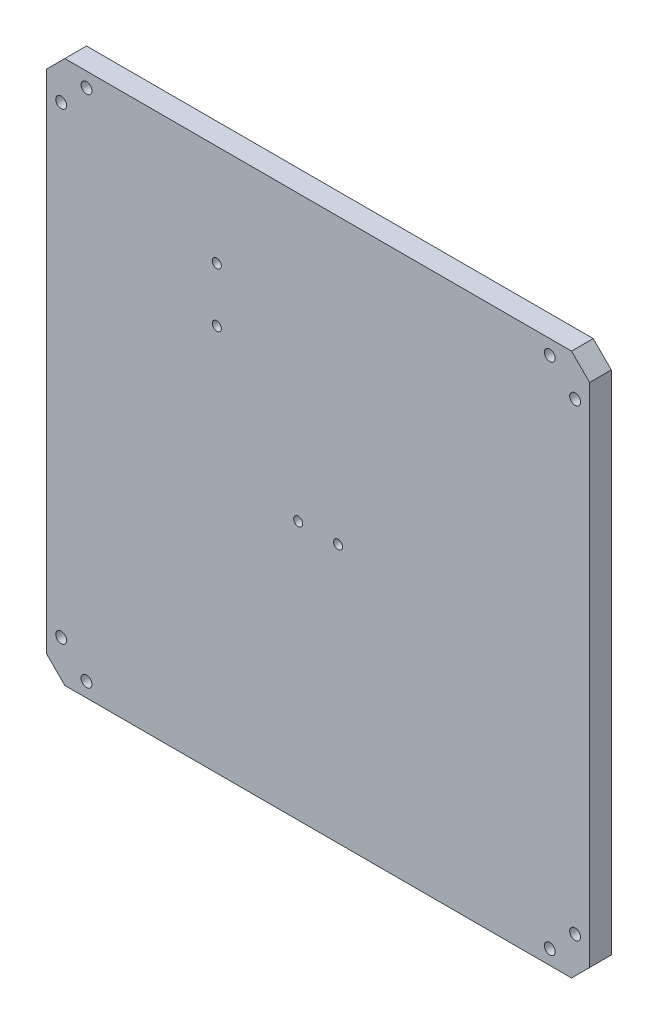
SolidWorks part; units mm, degrees
ref_plane "前视基准面" through (0, 0, 0) normal (0, 0, 1) x (1, 0, 0)
ref_plane "上视基准面" through (0, 0, 0) normal (0, 1, 0) x (1, 0, 0)
ref_plane "右视基准面" through (0, 0, 0) normal (1, 0, 0) x (0, 0, -1)
sketch "草图1" plane through (0, 0, 0) normal (0, 0, 1) x (1, 0, 0)
  line L1 (75, -75) -> (-75, -75)
  line L2 (75, -75) -> (75, 75)
  line L3 (75, 75) -> (-75, 75)
  line L4 (-75, -75) -> (-75, 75)
  line L5 (75, -75) -> (-75, 75) construction
  line L6 (75, 75) -> (-75, -75) construction
  point P0 (0, 0)
  dimension "D1" = 150
  dimension "D2" = 150
extrude "凸台-拉伸1" add sketch "草图1" along normal blind 6
chamfer "倒角1" distance 5 angle 45 4 edges at (75, -75, 3) (-75, -75, 3) (-75, 75, 3) (75, 75, 3)
sketch "草图2" plane through (0, 0, 6) normal (0, 0, 1) x (1, 0, 0)
  line L0 (75, -70) -> (75, 70) construction
  line L1 (70, 75) -> (-70, 75) construction
  line L2 (0, 110.4594) -> (0, -112.1687) construction
  circle A0 centre (64, 71) radius 1.5
  circle A1 centre (71, 64) radius 1.5
  circle A2 centre (-71, 64) radius 1.5
  circle A3 centre (-64, 71) radius 1.5
  dimension "D1" = 3
  dimension "D2" = 3
  dimension "D3" = 4
  dimension "D4" = 11
  dimension "D5" = 4
  dimension "D6" = 11
extrude "切除-拉伸1" cut sketch "草图2" against normal blind 10
sketch "草图3" plane through (0, 0, 0) normal (0, 0, -1) x (-1, 0, 0)
  line L0 (75, 70) -> (75, -70) construction
  line L1 (-70, 75) -> (70, 75) construction
  circle A0 centre (64, 71) radius 2.85
  circle A1 centre (71, 64) radius 2.85
  dimension "D1" = 5.7
  dimension "D2" = 4
  dimension "D3" = 11
  dimension "D4" = 4
  dimension "D5" = 11
extrude "切除-拉伸2" cut sketch "草图3" against normal blind 3.2
mirror "镜向1" about plane through (0, 0, 0) normal (1, 0, 0) of "切除-拉伸2"
mirror "镜向2" about plane through (0, 0, 0) normal (0, 1, 0) of "切除-拉伸1", "镜向1", "切除-拉伸2"
hole_wizard "M3 螺纹孔1" positions "草图4" profile "草图5" tap size "M3" standard "GB"
sketch "草图4" plane through (0, 0, 6) normal (0, 0, 1) x (1, 0, 0)
  point P0 (-5.5, -3.5)
  point P2 (5.5, -3.5)
sketch "草图5" plane through (-5.5, -3.5, 6) normal (1, 0, 0) x (0, -1, 0)
  line L0 (0, 0) -> (0, 8.2511)
  line L1 (0, 8.2511) -> (1.25, 7.5)
  line L2 (1.25, 7.5) -> (1.25, 0)
  line L5 (1.25, 0) -> (0, 0)
  line L10 (0, 8.2511) -> (-1.25, 7.5) construction
  line L11 (0, -6.35) -> (0, 107.95) construction
  dimension "螺纹孔钻头直径" = 2.5
  dimension "螺纹孔钻头深度" = 7.5
  dimension "导头角度" = 118
cosmetic thread "孔螺蚊线1" parameters "D1"=6, "D2"=3
cosmetic thread "孔螺蚊线2" parameters "D1"=6, "D2"=3
hole_wizard "M3 螺纹孔2" positions "草图8" profile "草图7" tap size "M3" standard "GB"
sketch "草图8" plane through (0, 0, 6) normal (0, 0, 1) x (1, 0, 0)
  point P0 (-28, 47)
  point P2 (-28, 32)
sketch "草图7" plane through (-28, 47, 6) normal (1, 0, 0) x (0, -1, 0)
  line L0 (0, 0) -> (0, 8.2511)
  line L1 (0, 8.2511) -> (1.25, 7.5)
  line L2 (1.25, 7.5) -> (1.25, 0)
  line L5 (1.25, 0) -> (0, 0)
  line L10 (0, 8.2511) -> (-1.25, 7.5) construction
  line L11 (0, -6.35) -> (0, 107.95) construction
  dimension "螺纹孔钻头直径" = 2.5
  dimension "螺纹孔钻头深度" = 7.5
  dimension "导头角度" = 118
cosmetic thread "孔螺蚊线3" parameters "D1"=6, "D2"=3
cosmetic thread "孔螺蚊线4" parameters "D1"=6, "D2"=3
